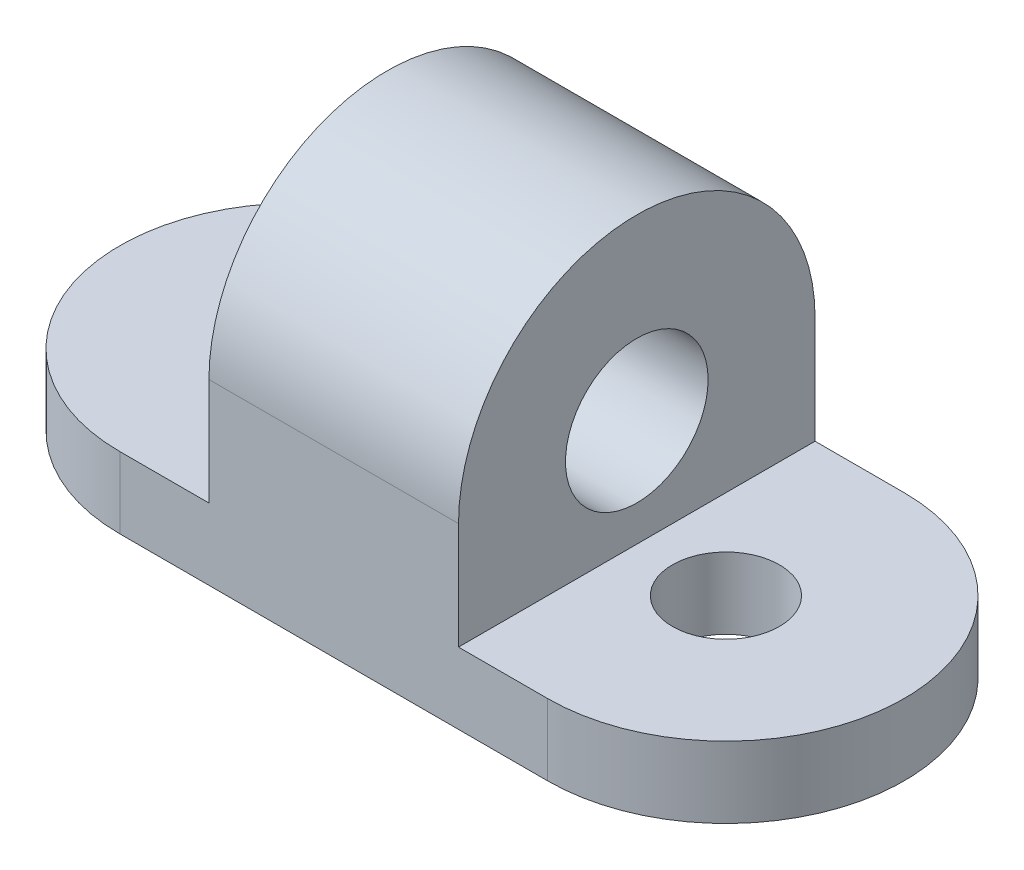
SolidWorks part; units mm, degrees
material "Copper"
ref_plane "Front Plane" through (0, 0, 0) normal (0, 0, 1) x (1, 0, 0)
ref_plane "Top Plane" through (0, 0, 0) normal (0, 1, 0) x (1, 0, 0)
ref_plane "Right Plane" through (0, 0, 0) normal (1, 0, 0) x (0, 0, -1)
sketch "Sketch1" plane through (0, 0, 0) normal (0, 1, 0) x (1, 0, 0)
  line L0 (-38.1, 31.75) -> (38.1, 31.75)
  line L1 (38.1, -31.75) -> (-38.1, -31.75)
  line L2 (0, 31.75) -> (0, -31.75) construction
  arc A0 (-38.1, -31.75) -> (-38.1, 31.75) centre (-38.1, 0) cw
  arc A1 (38.1, -31.75) -> (38.1, 31.75) centre (38.1, 0) ccw
  circle A2 centre (-38.1, 0) radius 9.525
  circle A3 centre (38.1, 0) radius 9.525
  point P10 (0, 0)
  dimension "D2" = 19.05
  dimension "D3" = 31.75
  dimension "D1" = 76.2
extrude "Boss-Extrude2" add sketch "Sketch1" along normal blind 12.7
sketch "Sketch2" plane through (0, 12.7, 0) normal (0, 1, 0) x (1, 0, 0)
  line L0 (38.1, 31.75) -> (-38.1, 31.75) construction
  line L1 (-22.225, 31.75) -> (22.225, 31.75)
  line L2 (-22.225, 31.75) -> (-22.225, -31.75)
  line L3 (-22.225, -31.75) -> (22.225, -31.75)
  line L4 (22.225, 31.75) -> (22.225, -31.75)
  line L5 (-38.1, -31.75) -> (38.1, -31.75) construction
  point P8 (0, 31.75)
  dimension "D1" = 44.45
extrude "Boss-Extrude3" add sketch "Sketch2" along normal blind 19.05
sketch "Sketch3" plane through (22.225, 0, 0) normal (1, 0, 0) x (0, 0, -1)
  line L4 (-31.75, 12.7) -> (31.75, 12.7)
  line L5 (31.75, 12.7) -> (31.75, 31.75)
  line L6 (31.75, 31.75) -> (-31.75, 31.75)
  line L7 (-31.75, 31.75) -> (-31.75, 12.7)
  line L8 (-31.75, 12.7) -> (31.75, 12.7)
  line L9 (31.75, 12.7) -> (31.75, 31.75)
  line L11 (-31.75, 31.75) -> (-31.75, 12.7)
  arc A0 (-31.75, 31.75) -> (31.75, 31.75) centre (0, 31.75) cw
  dimension "D1" = 0
extrude "Boss-Extrude4" add sketch "Sketch3" against normal blind 44.45
sketch "Sketch4" plane through (22.225, 0, 0) normal (1, 0, 0) x (0, 0, -1)
  line L0 (-31.75, 31.75) -> (31.75, 31.75) construction
  line L1 (31.75, 31.75) -> (31.75, 12.7) construction
  arc A0 (31.75, 31.75) -> (-31.75, 31.75) centre (0, 31.75) ccw construction
  circle A1 centre (0, 31.75) radius 12.7
  dimension "D1" = 25.4
extrude "Cut-Extrude1" cut sketch "Sketch4" against normal blind 44.45
